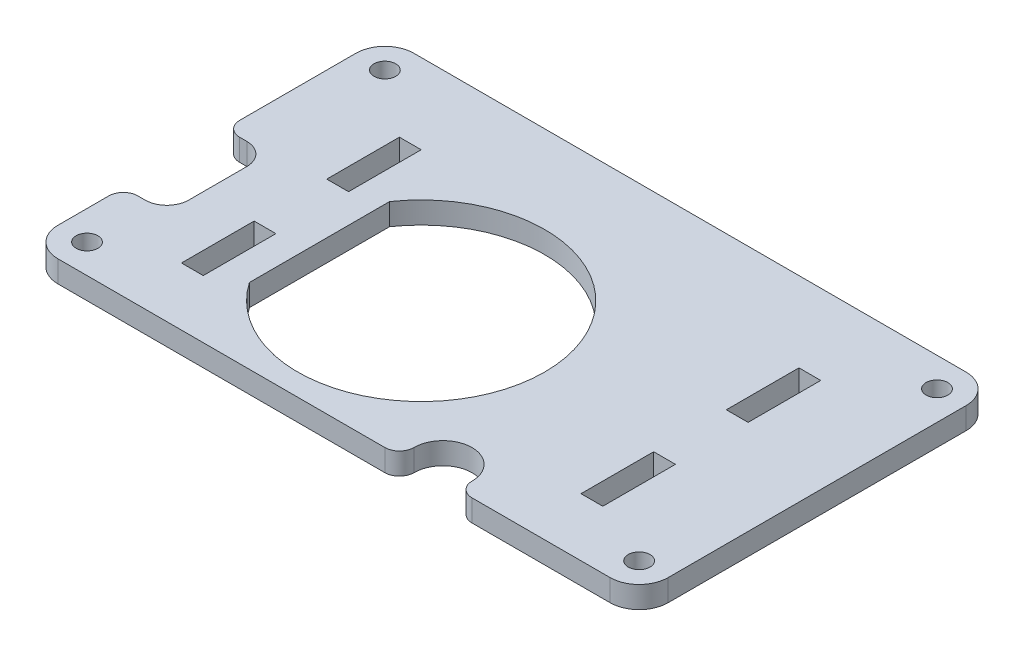
SolidWorks part; units mm, degrees
ref_plane "Front Plane" through (0, 0, 0) normal (0, 0, 1) x (1, 0, 0)
ref_plane "Top Plane" through (0, 0, 0) normal (0, 1, 0) x (1, 0, 0)
ref_plane "Right Plane" through (0, 0, 0) normal (1, 0, 0) x (0, 0, -1)
sketch "Sketch1" plane through (0, 0, 0) normal (0, 1, 0) x (1, 0, 0)
  line L0 (0, 0) -> (0, -31.4697) construction
  line L1 (26, 3.2274) -> (29, 3.2274)
  line L2 (26, 23.2274) -> (29, 23.2274)
  line L3 (26, 23.2274) -> (26, 13.2274)
  line L4 (26, 13.2274) -> (29, 13.2274)
  line L5 (29, 23.2274) -> (29, 13.2274)
  line L6 (26, 3.2274) -> (26, -6.7726)
  line L7 (26, -6.7726) -> (29, -6.7726)
  line L8 (29, 3.2274) -> (29, -6.7726)
  line L9 (-26, 23.2274) -> (-29, 23.2274)
  line L10 (-29, 23.2274) -> (-29, 13.2274)
  line L11 (-26, 23.2274) -> (-26, 13.2274)
  line L12 (-26, 13.2274) -> (-29, 13.2274)
  line L13 (-26, 3.2274) -> (-29, 3.2274)
  line L14 (-26, 3.2274) -> (-26, -6.7726)
  line L15 (-26, -6.7726) -> (-29, -6.7726)
  line L16 (-29, 3.2274) -> (-29, -6.7726)
  line L17 (-42, 30.2274) -> (-42, 14.2274)
  line L18 (-38, 34.2274) -> (38, 34.2274)
  line L19 (0, 0) -> (0, -14.7726)
  line L20 (-38, -14.7726) -> (7, -14.7726)
  line L21 (42, 30.2274) -> (42, -10.7726)
  line L22 (19, -14.7726) -> (38, -14.7726)
  line L23 (-36, 9.2274) -> (-36, 1.2274)
  line L24 (-39, 12.2274) -> (-40, 12.2274)
  line L25 (-39, -1.7726) -> (-40, -1.7726)
  line L26 (-42, -3.7726) -> (-42, -10.7726)
  line L27 (-22, -4.4162) -> (-22, 14.8711)
  circle A0 centre (38, 30.2274) radius 1.5
  circle A1 centre (38, -10.7726) radius 1.5
  circle A2 centre (-38, -10.7726) radius 1.5
  circle A3 centre (-38, 30.2274) radius 1.5
  arc A4 (42, 30.2274) -> (38, 34.2274) centre (38, 30.2274) ccw
  arc A5 (38, -14.7726) -> (42, -10.7726) centre (38, -10.7726) ccw
  arc A6 (-38, -14.7726) -> (-42, -10.7726) centre (-38, -10.7726) cw
  arc A7 (-42, 30.2274) -> (-38, 34.2274) centre (-38, 30.2274) cw
  arc A8 (17, -12.7726) -> (9, -12.7726) centre (13, -12.7726) ccw
  arc A9 (7, -14.7726) -> (9, -12.7726) centre (7, -12.7726) ccw
  arc A10 (17, -12.7726) -> (19, -14.7726) centre (19, -12.7726) ccw
  arc A11 (-39, -1.7726) -> (-36, 1.2274) centre (-39, 1.2274) ccw
  arc A12 (-36, 9.2274) -> (-39, 12.2274) centre (-39, 9.2274) ccw
  arc A13 (-42, 14.2274) -> (-40, 12.2274) centre (-40, 14.2274) ccw
  arc A14 (-40, -1.7726) -> (-42, -3.7726) centre (-40, -3.7726) ccw
  arc A15 (-22, -4.4162) -> (-22, 14.8711) centre (-8, 5.2274) ccw
  dimension "D1" = 4
  dimension "D2" = 41
  dimension "D11" = 25
  dimension "D12" = 12
  dimension "D13" = 6
  dimension "D16" = 30
  dimension "D17" = 41
  dimension "D18" = 4
  dimension "D19" = 34
  dimension "D3" = 26
  dimension "D4" = 7
  dimension "D5" = 10
  dimension "D6" = 3
  dimension "D7" = 10
  dimension "D8" = 4
  dimension "D9" = 4
  dimension "D10" = 2
  dimension "D14" = 3
  dimension "D15" = 8
  dimension "D20" = 20
extrude "Boss-Extrude2" add sketch "Sketch1" along normal blind 3
